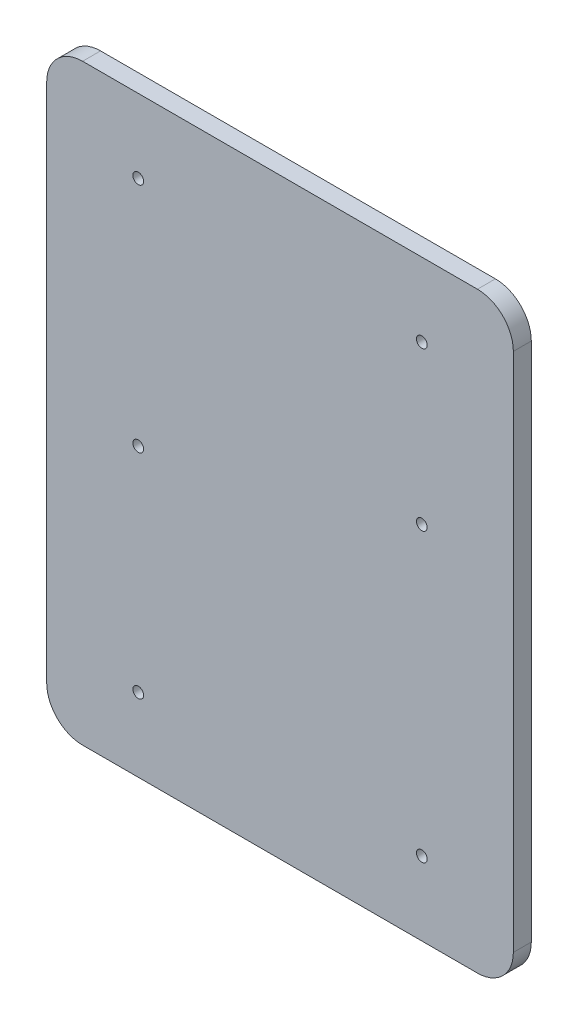
SolidWorks part; units mm, degrees
material "Acrílico (médio-alto impacto)"
ref_plane "Plano frontal" through (0, 0, 0) normal (0, 0, 1) x (1, 0, 0)
ref_plane "Plano superior" through (0, 0, 0) normal (0, 1, 0) x (1, 0, 0)
ref_plane "Plano direito" through (0, 0, 0) normal (1, 0, 0) x (0, 0, -1)
sketch "Esboço1" plane through (0, 0, 0) normal (0, 0, 1) x (1, 0, 0)
  line L1 (-49.2171, -36.3939) -> (60.7829, -36.3939)
  line L2 (-59.2171, -26.3939) -> (-59.2171, 118.6061)
  line L3 (-49.2171, 128.6061) -> (60.7829, 128.6061)
  line L4 (70.7829, -26.3939) -> (70.7829, 118.6061)
  arc A0 (-59.2171, 118.6061) -> (-49.2171, 128.6061) centre (-49.2171, 118.6061) cw
  arc A1 (60.7829, 128.6061) -> (70.7829, 118.6061) centre (60.7829, 118.6061) cw
  arc A2 (60.7829, -36.3939) -> (70.7829, -26.3939) centre (60.7829, -26.3939) ccw
  arc A3 (-49.2171, -36.3939) -> (-59.2171, -26.3939) centre (-49.2171, -26.3939) cw
  dimension "D1" = 10
extrude "Ressalto-extrusão1" add sketch "Esboço1" along normal blind 5
sketch "Esboço2" plane through (0, 0, 0) normal (0, 0, -1) x (-1, 0, 0)
  line L1 (-70.7829, -26.3939) -> (-70.7829, 118.6061) construction
  line L2 (59.2171, 118.6061) -> (59.2171, -26.3939) construction
  line L4 (-60.7829, 128.6061) -> (49.2171, 128.6061) construction
  circle A0 centre (33.7171, -15.8939) radius 1.5
  circle A1 centre (33.7171, 108.1061) radius 1.5
  circle A2 centre (-45.2829, -15.8939) radius 1.5
  circle A3 centre (-45.2829, 108.1061) radius 1.5
  dimension "D1" = 79
  dimension "D2" = 124
  dimension "D3" = 124
  dimension "D4" = 79
  dimension "D5" = 3
  dimension "D6" = 3
  dimension "D7" = 3
  dimension "D8" = 3
  dimension "D9" = 25.5
  dimension "D10" = 25.5
  dimension "D11" = 25.5
  dimension "D12" = 25.5
  dimension "D13" = 20.5
extrude "Corte-extrusão1" cut sketch "Esboço2" against normal blind 5
sketch "Esboço3" plane through (0, 0, 0) normal (0, 0, -1) x (-1, 0, 0)
  line L1 (59.2171, 118.6061) -> (59.2171, -26.3939) construction
  circle A1 centre (33.7171, 43.5061) radius 1.5
  circle A2 centre (33.7171, 108.1061) radius 1.5 construction
  point P2 (0, 0)
  dimension "D1" = 64.6
  dimension "D3" = 3
  dimension "D5" = 25.5
extrude "Corte-extrusão2" cut sketch "Esboço3" against normal through all
sketch "Esboço9" plane through (0, 0, 0) normal (0, 0, -1) x (-1, 0, 0)
  line L1 (-70.7829, -26.3939) -> (-70.7829, 118.6061) construction
  circle A0 centre (-45.2829, 64.1061) radius 1.5
  circle A3 centre (-45.2829, 108.1061) radius 1.5 construction
  dimension "D1" = 3
  dimension "D2" = 25.5
  dimension "D3" = 44
extrude "Corte-extrusão7" cut sketch "Esboço9" against normal blind 10
